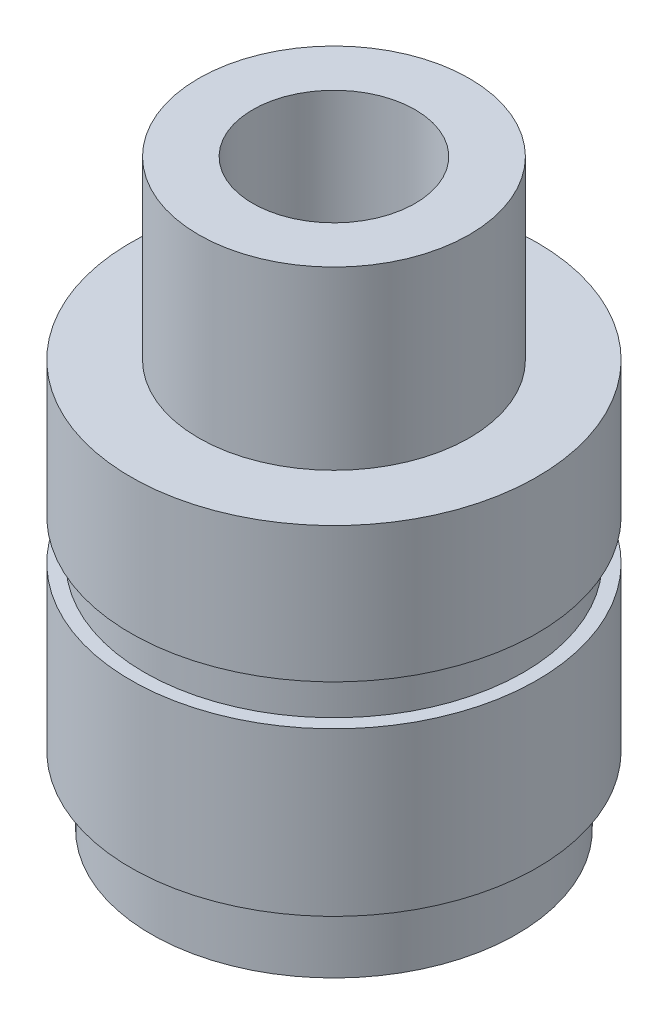
SolidWorks part; units mm, degrees
ref_plane "前视基准面" through (0, 0, 0) normal (0, 0, 1) x (1, 0, 0)
ref_plane "上视基准面" through (0, 0, 0) normal (0, 1, 0) x (1, 0, 0)
ref_plane "右视基准面" through (0, 0, 0) normal (1, 0, 0) x (0, 0, -1)
other "Configuration Table"
sketch "草图1" plane through (0, 0, 0) normal (0, 0, 1) x (1, 0, 0)
  line L0 (12, 0) -> (12, 25)
  line L1 (12, 25) -> (6, 25)
  line L2 (6, 25) -> (6, 43)
  line L3 (6, 43) -> (10, 43)
  line L4 (10, 43) -> (10, 30)
  line L5 (10, 30) -> (15, 30)
  line L6 (15, 30) -> (15, 20)
  line L7 (15, 20) -> (14, 20)
  line L8 (14, 20) -> (14, 17)
  line L9 (14, 17) -> (15, 17)
  line L10 (15, 17) -> (15, 5)
  line L11 (15, 5) -> (13.5, 5)
  line L12 (13.5, 5) -> (13.5, 0)
  line L13 (13.5, 0) -> (12, 0)
  line L14 (0, 0) -> (0, 40.4336) construction
  point P17 (0, 0)
  point P18 (0, 40.4336)
  dimension "D1" = 12
  dimension "D2" = 13.5
  dimension "D3" = 15
  dimension "D4" = 3
  dimension "D5" = 10
  dimension "D6" = 30
  dimension "D7" = 5
  dimension "D8" = 0
  dimension "D9" = 15
  dimension "D10" = 14
  dimension "D11" = 10
  dimension "D12" = 6
  dimension "D13" = 25
  dimension "D14" = 13
revolve "旋转1" add sketch "草图1" angle 360 about L14
